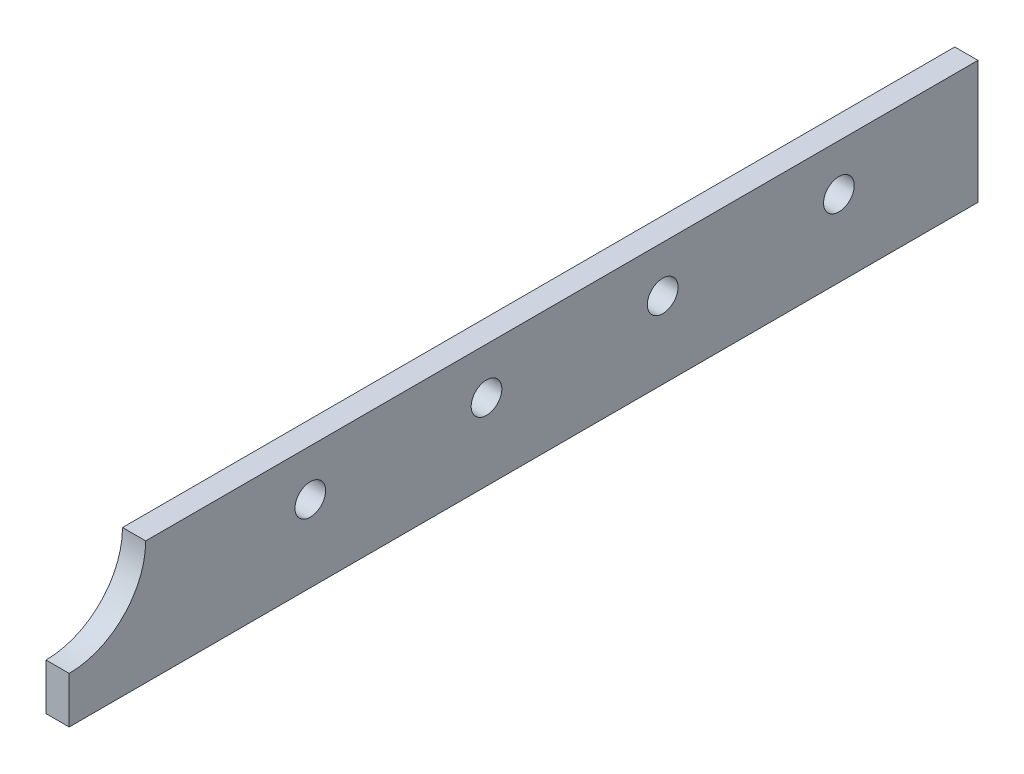
SolidWorks part; units mm, degrees
material "Silicon Rubber"
ref_plane "Front Plane" through (0, 0, 0) normal (0, 0, 1) x (1, 0, 0)
ref_plane "Top Plane" through (0, 0, 0) normal (0, 1, 0) x (1, 0, 0)
ref_plane "Right Plane" through (0, 0, 0) normal (1, 0, 0) x (0, 0, -1)
sketch "Sketch1" plane through (0, 0, 0) normal (1, 0, 0) x (0, 0, -1)
  line L13 (-62.23, -8.4201) -> (62.23, -8.4201)
  line L14 (-62.23, -8.4201) -> (-62.23, -2.0574)
  line L15 (-51.7525, 8.4201) -> (62.23, 8.4201)
  line L16 (62.23, -8.4201) -> (62.23, 8.4201)
  line L17 (-62.23, -8.4201) -> (62.23, 8.4201) construction
  line L18 (-62.23, 8.4201) -> (62.23, -8.4201) construction
  arc A0 (-62.23, -2.0574) -> (-51.7525, 8.4201) centre (-62.23, 8.4201) ccw
  point P0 (0, 0)
  dimension "D2" = 124.46
  dimension "D3" = 20.955
  dimension "D1" = 16.8402
  dimension "D4" = 10.4775
  dimension "D5" = 6.3627
extrude "Boss-Extrude1" add sketch "Sketch1" along normal blind 3.175
sketch "Sketch3" plane through (0, 0, 0) normal (-1, 0, 0) x (0, 0, 1)
  line L0 (-62.23, 8.4201) -> (-62.23, -4.2799) construction
  line L1 (-62.23, -8.4201) -> (-62.23, 8.4201) construction
  line L2 (-62.23, 2.0701) -> (53.896, 2.0701) construction
  arc A0 (51.7525, 8.4201) -> (62.23, -2.0574) centre (62.23, 8.4201) ccw construction
  circle A1 centre (-43.18, 2.0701) radius 2.1
  circle A2 centre (-19.05, 2.0701) radius 2.1
  circle A3 centre (5.08, 2.0701) radius 2.1
  circle A4 centre (29.21, 2.0701) radius 2.1
  dimension "D2" = 4.2
  dimension "D3" = 19.05
  dimension "D1" = 12.7
  dimension "D4" = 24.13
  dimension "D5" = 24.13
  dimension "D6" = 24.13
extrude "Cut-Extrude1" cut sketch "Sketch3" against normal through all
